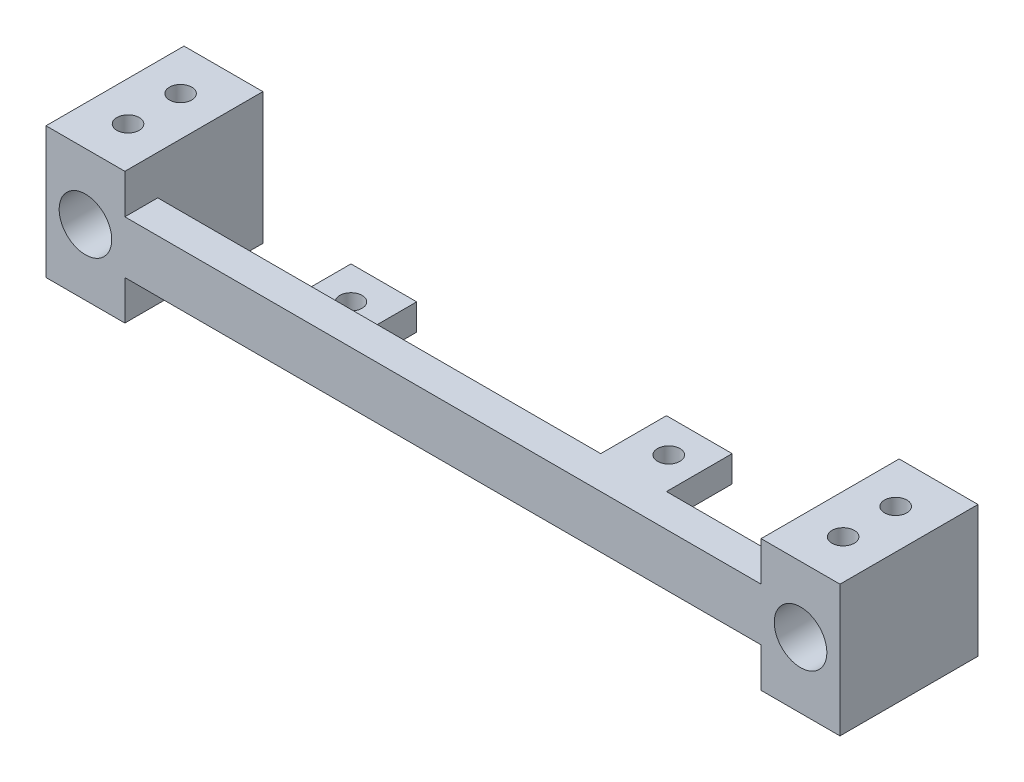
SolidWorks part; units mm, degrees
ref_plane "Plan de face" through (0, 0, 0) normal (0, 0, 1) x (1, 0, 0)
ref_plane "Plan de dessus" through (0, 0, 0) normal (0, 1, 0) x (1, 0, 0)
ref_plane "Plan de droite" through (0, 0, 0) normal (1, 0, 0) x (0, 0, -1)
sketch "Esquisse1" plane through (0, 0, 0) normal (0, 0, 1) x (1, 0, 0)
  line L1 (-60.4, -4) -> (60.4, -4)
  line L2 (-60.4, -4) -> (-60.4, 4)
  line L3 (-60.4, 4) -> (60.4, 4)
  line L4 (60.4, -4) -> (60.4, 4)
  line L5 (-60.4, -4) -> (60.4, 4) construction
  line L6 (-60.4, 4) -> (60.4, -4) construction
  point P0 (0, 0)
  dimension "D1" = 120.8
  dimension "D2" = 8
extrude "Boss.-Extru.1" add sketch "Esquisse1" along normal blind 5
sketch "Esquisse2" plane through (0, 0, 0) normal (0, 0, -1) x (-1, 0, 0)
  line L0 (0, -4) -> (0, 4) construction
  line L1 (60.4, -4) -> (-60.4, -4) construction
  line L2 (-60.4, 4) -> (60.4, 4) construction
  line L3 (24.175, 4) -> (24.175, -4) construction
  line L4 (-24.175, 4) -> (-24.175, -4) construction
  line L5 (19, -4) -> (19, 0) construction
  line L6 (-19, 0) -> (-19, 4) construction
  line L8 (19, -4) -> (29, -4)
  line L9 (19, -4) -> (19, 0)
  line L10 (19, 0) -> (29, 0)
  line L11 (29, -4) -> (29, 0)
  line L12 (-19, 0) -> (-29, 0)
  line L13 (-19, 0) -> (-19, 4)
  line L14 (-19, 4) -> (-29, 4)
  line L15 (-29, 0) -> (-29, 4)
  dimension "D1" = 24.175
  dimension "D2" = 19
  dimension "D3" = 4
  dimension "D4" = 4
  dimension "D5" = 10
  dimension "D6" = 10
  dimension "D7" = 19
extrude "Boss.-Extru.2" add sketch "Esquisse2" along normal blind 10
sketch "Esquisse3" plane through (0, 4, 0) normal (0, 1, 0) x (1, 0, 0)
  circle A0 centre (-24, 5) radius 1.7
  circle A1 centre (24.35, 5) radius 1.7
  dimension "D1" = 48.35
extrude "Enlèv. mat.-Extru.1" cut sketch "Esquisse3" against normal blind 10
sketch "Esquisse4" plane through (0, 0, 0) normal (0, 0, -1) x (-1, 0, 0)
  line L0 (54.4, 4) -> (54.4, -4) construction
  line L1 (-19, 4) -> (60.4, 4) construction
  line L2 (60.4, -4) -> (29, -4) construction
  line L3 (60.4, 4) -> (60.4, -4) construction
  line L4 (0, -4) -> (0, 4) construction
  line L5 (48.4, 10) -> (60.4, 10)
  line L6 (48.4, 10) -> (48.4, -10)
  line L7 (48.4, -10) -> (60.4, -10)
  line L8 (60.4, 10) -> (60.4, -10)
  line L9 (48.4, 10) -> (60.4, -10) construction
  line L10 (48.4, -10) -> (60.4, 10) construction
  line L11 (19, -4) -> (-60.4, -4) construction
  line L12 (-60.4, 10) -> (-60.4, -10)
  line L13 (-48.4, -10) -> (-60.4, -10)
  line L14 (-48.4, 10) -> (-48.4, -10)
  line L15 (-48.4, 10) -> (-60.4, 10)
  point P8 (54.4, 0)
  dimension "D1" = 6
  dimension "D2" = 20
extrude "Boss.-Extru.3" add sketch "Esquisse4" along normal blind 16 and the other way blind 5
sketch "Esquisse5" plane through (0, 0, -16) normal (0, 0, -1) x (-1, 0, 0)
  line L0 (0, 4) -> (0, -4) construction
  line L1 (-19, 4) -> (48.4, 4) construction
  line L2 (19, -4) -> (-48.4, -4) construction
  circle A0 centre (54.4, 0) radius 4
  circle A1 centre (-54.4, 0) radius 4
extrude "Enlèv. mat.-Extru.2" cut sketch "Esquisse5" against normal blind 24
sketch "Esquisse6" plane through (0, -10, 0) normal (0, -1, 0) x (1, 0, 0)
  line L0 (0, 5) -> (0, -2.8733) construction
  line L1 (-48.4, 5) -> (48.4, 5) construction
  circle A0 centre (54.4, -9.479) radius 1.7
  circle A1 centre (54.4, -1.479) radius 1.7
  circle A2 centre (-54.4, -1.479) radius 1.7
  circle A3 centre (-54.4, -9.479) radius 1.7
  dimension "D1" = 8
extrude "Enlèv. mat.-Extru.3" cut sketch "Esquisse6" against normal blind 24
